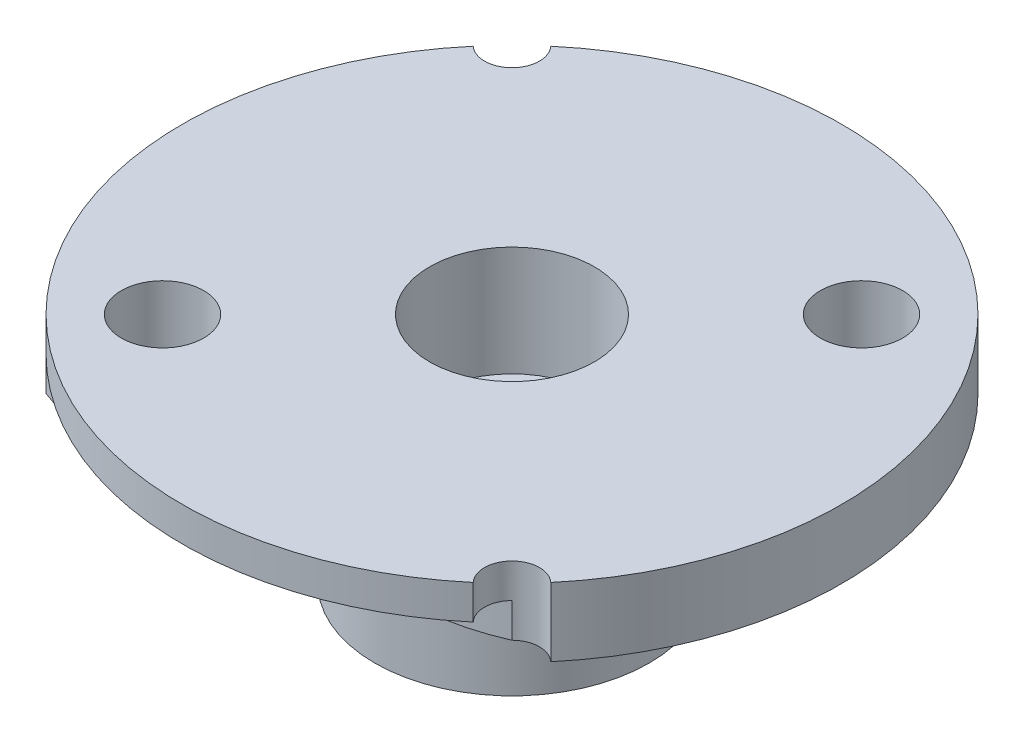
SolidWorks part; units mm, degrees
ref_plane "Alzado" through (0, 0, 0) normal (0, 0, 1) x (1, 0, 0)
ref_plane "Planta" through (0, 0, 0) normal (0, 1, 0) x (1, 0, 0)
ref_plane "Vista lateral" through (0, 0, 0) normal (1, 0, 0) x (0, 0, -1)
sketch "Croquis1" plane through (0, 0, 0) normal (0, 1, 0) x (1, 0, 0)
  circle A0 centre (0, 0) radius 12
  dimension "D1" = 24
extrude "Saliente-Extruir1" add sketch "Croquis1" along normal blind 2.5
sketch "Croquis2" plane through (0, 2.5, 0) normal (0, 1, 0) x (1, 0, 0)
  circle A0 centre (0, 0) radius 3.0015
sketch "Croquis3" plane through (0, 0, 0) normal (0, -1, 0) x (1, 0, 0)
  circle A0 centre (0, 0) radius 5
  dimension "D1" = 10
extrude "Saliente-Extruir2" add sketch "Croquis3" along normal blind 6
extrude "Cortar-Extruir1" cut sketch "Croquis2" against normal blind 4
sketch "Croquis4" plane through (0, -1.5, 0) normal (0, 1, 0) x (1, 0, 0)
  circle A1 centre (0, 0) radius 1.5
  dimension "D1" = 3
extrude "Cortar-Extruir2" cut sketch "Croquis4" against normal blind 8
sketch "Croquis5" plane through (0, -6, 0) normal (0, -1, 0) x (1, 0, 0)
  circle A0 centre (0, 0) radius 2
  dimension "D1" = 4
extrude "Cortar-Extruir6" cut sketch "Croquis5" against normal blind 4
sketch "Croquis6" plane through (0, 2.5, 0) normal (0, 1, 0) x (1, 0, 0)
  circle A1 centre (6.364, 6.364) radius 1.5
  circle A2 centre (-6.364, -6.364) radius 1.5
extrude "Cortar-Extruir7" cut sketch "Croquis6" against normal blind 4
sketch "Croquis7" plane through (0, 0, 0) normal (0, -1, 0) x (1, 0, 0)
  circle A0 centre (0, 0) radius 12 construction
  circle A1 centre (8.4853, 8.4853) radius 1
  circle A2 centre (-8.4853, -8.4853) radius 1
  point P7 (0, 0)
  dimension "D1" = 2
  dimension "D2" = 2
extrude "Cortar-Extruir8" cut sketch "Croquis7" against normal blind 4
sketch "Croquis8" plane through (0, 0, 0) normal (0, -1, 0) x (1, 0, 0)
  arc A0 (7.7493, 9.1623) -> (9.1623, 7.7493) centre (8.4853, 8.4853) ccw construction
  arc A1 (7.7493, 9.1623) -> (-9.1623, -7.7493) centre (0, 0) ccw construction
  arc A2 (7.7493, 9.1623) -> (7.7782, 7.7782) centre (8.4853, 8.4853) ccw
  arc A3 (7.7493, 9.1623) -> (-8.4853, 8.4853) centre (0, 0) ccw
  arc A4 (-7.7493, -9.1623) -> (-9.1623, -7.7493) centre (-8.4853, -8.4853) ccw construction
  arc A5 (-7.7493, -9.1623) -> (9.1623, 7.7493) centre (0, 0) ccw construction
  arc A6 (-7.7493, -9.1623) -> (8.4853, -8.4853) centre (0, 0) ccw
  arc A7 (-7.7493, -9.1623) -> (-7.7782, -7.7782) centre (-8.4853, -8.4853) ccw
  arc A8 (7.7493, 9.1623) -> (-8.4853, 8.4853) centre (0, 0) ccw
  spline S0 degree 3 poles (7.7782, 7.7782) (6.0438, 8.5533) (1.9385, 8.6834) (-2.1147, 7.906) (-3.9671, 6.4786) knots 0 0 0 0 0.452401 1 1 1 1
  spline S1 degree 3 poles (-7.7782, -7.7782) (-4.1688, -9.2735) (0.2233, -9.4116) (3.5486, -6.9179) knots 0 0 0 0 1 1 1 1
  spline S2 degree 3 poles (8.4853, -8.4853) (7.7613, -8.8182) (6.4483, -9.0913) (4.851, -8.3123) (4.1155, -7.4258) (3.9665, -6.4787) (3.5486, -6.9179) knots 0 0 0 0 0.40762 0.622914 0.853293 1 1 1 1
  spline S3 degree 3 poles (-8.4853, 8.4853) (-7.5927, 8.8451) (-6.3139, 9.0084) (-4.859, 8.387) (-4.2643, 7.6085) (-4.0728, 6.8676) (-4.1475, 6.3873) (-3.9671, 6.4786) knots 0 0 0 0 0.492099 0.601947 0.7881 0.955757 1 1 1 1
  arc M7 (7.7493, 9.1623) -> (-9.1623, -7.7493) centre (0, 0) ccw
  arc M8 (-9.1623, -7.7493) -> (-7.7493, -9.1623) centre (-8.4853, -8.4853) cw
  arc M9 (-7.7493, -9.1623) -> (9.1623, 7.7493) centre (0, 0) ccw
  arc M10 (9.1623, 7.7493) -> (7.7493, 9.1623) centre (8.4853, 8.4853) cw
extrude "Cortar-Extruir9" cut sketch "Croquis8" against normal blind 1.25 contours S3 S0 M7 M10 | S2 S1 M9 M8
